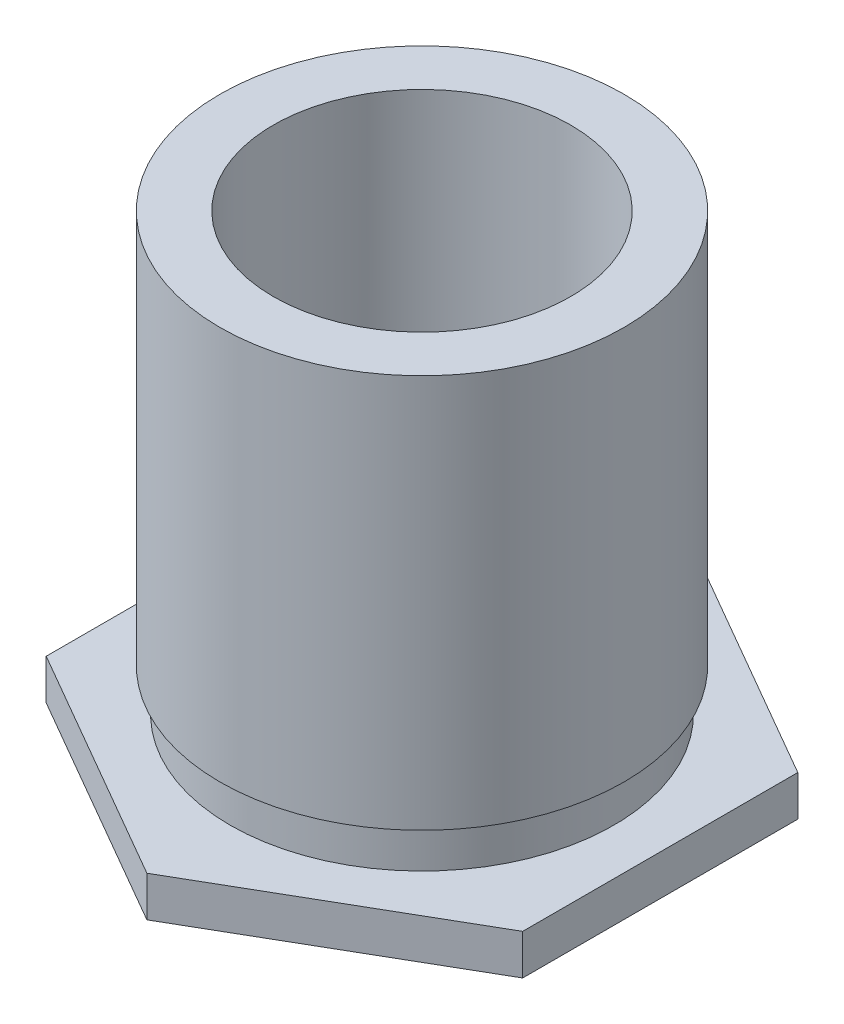
SolidWorks part; units mm, degrees
ref_plane "Plane1" through (0, 0, 0) normal (0, 0, 1) x (1, 0, 0)
ref_plane "Plane2" through (0, 0, 0) normal (0, 1, 0) x (1, 0, 0)
ref_plane "Plane3" through (0, 0, 0) normal (1, 0, 0) x (0, 0, -1)
sketch "BodySke" plane through (0, 0, 0) normal (0, 0, 1) x (1, 0, 0)
  line L0 (2.6924, 0) -> (3.683, 0)
  line L1 (3.683, 0) -> (3.683, 0.5385)
  line L2 (3.683, 0.5385) -> (2.5578, 0.5385)
  line L3 (1.3526, 6.35) -> (1.3526, 0.0051)
  line L4 (2.6924, 1.1039) -> (2.5578, 1.1039)
  line L5 (2.5578, 1.1039) -> (2.5578, 0.5385)
  line L6 (2.6924, 0.0025) -> (2.6924, 0)
  line L7 (1.016, 5.5575) -> (3.6522, 5.5575) construction
  line L8 (2.6924, 6.35) -> (1.3526, 6.35)
  line L9 (0, 0) -> (0, 15.24) construction
  line L10 (2.6924, 0.0025) -> (0, 0.0025)
  line L11 (2.6924, 6.35) -> (2.6924, 1.1039)
  line L12 (0, 0.0051) -> (1.3526, 0.0051)
  line L13 (0, 0.0051) -> (0, 0.0025)
  line L14 (1.016, 0.0051) -> (3.6522, 0.0051) construction
  line L15 (1.016, 0) -> (3.6522, 0) construction
  dimension "D1" = 0.0025
  dimension "E_dia" = 7.366
  dimension "C_dia" = 5.3848
  dimension "Thread_min" = 2.7051
  dimension "Clinching_ht" = 0.5385
  dimension "Advance" = 0.7925
  dimension "Length" = 6.35
  dimension "Thread_limit" = 6.3449
  dimension "Thread_depth" = 6.3449
  dimension "Drill_depth" = 6.35
  dimension "Groove_wid" = 0.5654
  dimension "Groove_dia" = 5.1156
revolve "Body" add sketch "BodySke"
cosmetic thread "ThreadCosmetic" [suppressed]
revolve "EndChamfer" cut sketch "EndChamferSke" angle 360 about L0
sketch "EndChamferSke" plane through (0, 0, 0) normal (0, 0, 1) x (1, 0, 0)
  line L0 (0, -2.54) -> (0, 7.62) construction
  line L1 (0, 0) -> (0, 15.24) construction
  line L2 (1.9812, 1.6002) -> (1.9812, 6.604)
  line L4 (1.9812, 1.6002) -> (1.7526, 1.6002)
  line L6 (1.7526, 1.6002) -> (1.3525, 1.3202)
  line L8 (1.3525, 1.3202) -> (1.3525, 6.604)
  line L9 (1.9812, 6.604) -> (1.3525, 6.604)
  line L10 (2.6924, 6.35) -> (-2.6924, 6.35) construction
  dimension "D1" = 0.254
  dimension "Thread_nominal" = 3.5052
  dimension "D2" = 34.99
  dimension "Thread_min" = 2.7051
  dimension "Inset" = 4.7498
  dimension "B_dia" = 3.9624
revolve "TapDrill" cut sketch "TapDriSke" angle 360 about L0
sketch "TapDriSke" plane through (0, 0, 0) normal (0, 0, 1) x (1, 0, 0)
  line L0 (0, 0) -> (0, 15.24) construction
  line L1 (0, 0) -> (0, 15.24) construction
  line L2 (1.3526, -3.9573) -> (1.3526, 6.35)
  line L3 (2.6924, 6.35) -> (-2.6924, 6.35) construction
  line L4 (1.3526, -3.9573) -> (0, -4.5176)
  line L5 (0, -4.5176) -> (0, 6.35)
  line L6 (0, 6.35) -> (1.3526, 6.35)
  line L7 (1.3526, 0.0051) -> (1.3526, 6.35) construction
  line L8 (0, -4.5176) -> (-1.3526, -3.9573) construction
  line L9 (-1.3526, 6.35) -> (-1.3526, 0.0051) construction
  dimension "D1" = 135
  dimension "Depth" = 10.3073
ref_plane "Plane4" through (0, -0.5486, 0) normal (0, 1, 0) x (-1, 0, 0)
sketch "ThdSchSke" plane through (0, 0, 0) normal (0, 0, 1) x (1, 0, 0)
  line L0 (0, -5.08) -> (0, 7.62) construction
  line L1 (0, 0) -> (0, 15.24) construction
  line L2 (0, 1.6002) -> (1.7526, 1.6002) construction
  line L4 (1.7526, 1.6002) -> (1.3526, 1.8803)
  line L5 (1.9812, 1.6002) -> (-1.9812, 1.6002) construction
  line L6 (1.7526, 1.6002) -> (1.3526, 1.3201)
  line L7 (1.3526, 1.8803) -> (1.3526, 1.3201)
  dimension "Vee_angle" = 70
  dimension "Thread_nominal" = 3.5052
  dimension "Thread_min" = 2.7051
revolve "ThreadSchematic" [suppressed] cut sketch "ThdSchSke" angle 360 about L0
pattern_linear "ThdSchPat" [suppressed]
sketch "HexDieSke" plane through (0, 0.5385, 0) normal (0, 1, 0) x (-1, 0, 0)
  line L0 (0, 3.6662) -> (3.175, 1.8331)
  line L1 (3.175, 1.8331) -> (3.175, -1.8331)
  line L2 (3.175, -1.8331) -> (0, -3.6662)
  line L3 (0, -3.6662) -> (-3.175, -1.8331)
  line L4 (-3.175, -1.8331) -> (-3.175, 1.8331)
  line L5 (-3.175, 1.8331) -> (0, 3.6662)
  circle A1 centre (0, 0) radius 3.175 construction
  circle A2 centre (0, 0) radius 3.6662 construction
  circle A3 centre (0, 0) radius 3.6957
  dimension "Width_across_flats" = 6.35
  dimension "OD" = 7.3914
extrude "HexDie" cut sketch "HexDieSke" against normal blind 0.5385
equation "' \"Length@BodySke\" = 0.75"
equation "' \"B_dia@EndChamferSke\" = 0.203"
equation "' \"C_dia@BodySke\" = 0.28"
equation "' \"Width_across_flats@HexDieSke\" = 0.312"
equation "' \"Inset@EndChamferSke\" = 0.312"
equation "' \"Advance@BodySke\" = 0.0312"
equation "' \"Thread_min@BodySke\" = 0.1528"
equation "' \"Thread_nominal@ThreadCosmetic\" = 0.19"
equation "\"E_dia@BodySke\" = \"Width_across_flats@HexDieSke\" * 1.16"
equation "\"Drill_depth@BodySke\" = \"Length@BodySke\""
equation "\"Thread_depth@BodySke\" = \"Length@BodySke\" - 0.0002"
equation "\"Clinching_ht@BodySke\" = \"C_dia@BodySke\" * 0.1"
equation "\"Groove_dia@BodySke\" = \"C_dia@BodySke\" * 0.95"
equation "\"Groove_wid@BodySke\" = \"Clinching_ht@BodySke\" * 1.05"
equation "\"Thread_limit@BodySke\" = ((sgn( \"Length@BodySke\" - \"Thread_depth@BodySke\" )-1)*( \"Length@BodySke\" - \"Thread_depth@BodySke\" ))/-2+ \"Thread_depth@BodySke\""
equation "\"Depth@TapDriSke\" = \"Thread_limit@BodySke\" + \"Advance@BodySke\" * 5"
equation "\"Depth@TapDriSke\" = ((sgn( \"Depth@TapDriSke\" - \"Drill_depth@BodySke\" )+1)*( \"Depth@TapDriSke\" - \"Drill_depth@BodySke\" ))/2 +\"Drill_depth@BodySke\""
equation "\"Depth@HexDie\" = \"Clinching_ht@BodySke\""
equation "\"OD@HexDieSke\" =  \"Width_across_flats@HexDieSke\" * 1.16 + 0.001"
equation "\"Thread_nominal@EndChamferSke\" = \"Thread_nominal@ThreadCosmetic\""
equation "\"Thread_min@EndChamferSke\" = \"Thread_min@BodySke\""
equation "\"D2@EndChamferSke\" = \"Vee_angle@ThdSchSke\" / 2 - 0.01"
equation "\"Thread_nominal@ThdSchSke\" = \"Thread_nominal@ThreadCosmetic\""
equation "\"Thread_min@ThdSchSke\" = \"Thread_min@BodySke\""
equation "\"Num_threads@ThdSchPat\" = int(  ( \"Thread_limit@BodySke\" - \"Inset@EndChamferSke\" ) / \"Advance@BodySke\" + 0.999 )  + 1"
equation "\"Advance@ThdSchPat\" = (  \"Thread_limit@BodySke\" - \"Inset@EndChamferSke\" ) /  (\"Num_threads@ThdSchPat\" - 1) 'relax it"
